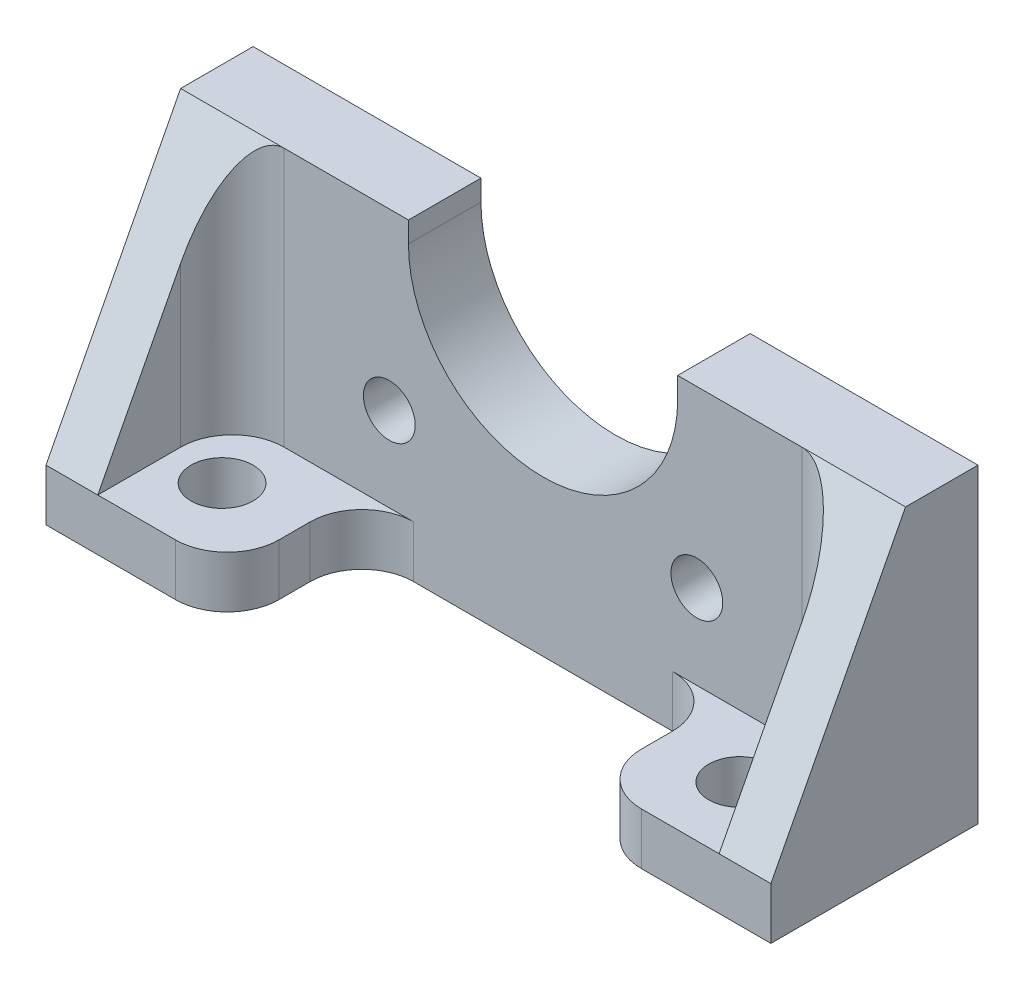
SolidWorks part; units mm, degrees
ref_plane "Front Plane" through (0, 0, 0) normal (0, 0, 1) x (1, 0, 0)
ref_plane "Top Plane" through (0, 0, 0) normal (0, 1, 0) x (1, 0, 0)
ref_plane "Right Plane" through (0, 0, 0) normal (1, 0, 0) x (0, 0, -1)
sketch "Sketch1" plane through (0, 0, 0) normal (0, 0, 1) x (1, 0, 0)
  line L0 (0, 0) -> (0, 5)
  line L1 (0, 5) -> (0, 30)
  line L2 (0, 30) -> (22, 30)
  line L3 (70, 30) -> (70, 5)
  line L4 (70, 5) -> (70, 0)
  line L5 (70, 0) -> (0, 0)
  line L6 (22, 28) -> (22, 30)
  line L7 (48, 28) -> (48, 30)
  line L8 (48, 30) -> (70, 30)
  line L9 (20.1508, 13.1508) -> (35, 28) construction
  line L10 (35, 28) -> (49.8492, 13.1508) construction
  arc A0 (22, 28) -> (48, 28) centre (35, 28) ccw
  circle A1 centre (20.1508, 13.1508) radius 2.5
  circle A2 centre (49.8492, 13.1508) radius 2.5
  circle A3 centre (35, 28) radius 21 construction
  dimension "D1" = 13
  dimension "D7" = 5
  dimension "D8" = 42
  dimension "D2" = 5
  dimension "D3" = 70
  dimension "D5" = 2
  dimension "D6" = 25
extrude "Boss-Extrude1" add sketch "Sketch1" along normal blind 20
sketch "Sketch2" plane through (70, 0, 0) normal (1, 0, 0) x (0, 0, -1)
  line L0 (-7, 30) -> (-20, 5)
  line L1 (-20, 30) -> (0, 30) construction
  line L2 (-20, 5) -> (-20, 30)
  line L3 (-20, 30) -> (-7, 30)
  line L4 (0, 0) -> (0, 30) construction
  line L5 (-20, 0) -> (-20, 30) construction
  line L6 (-20, 0) -> (0, 0) construction
  dimension "D1" = 7
  dimension "D2" = 5
extrude "Cut-Extrude1" cut sketch "Sketch2" against normal through all
sketch "Sketch3" plane through (0, 0, 0) normal (0, -1, 0) x (1, 0, 0)
  line L0 (10, 13) -> (60, 13) construction
  line L3 (35, 13) -> (35, 0) construction
  line L4 (0, 0) -> (70, 0) construction
  line L5 (0, 20) -> (70, 20) construction
  line L6 (17.5, 20) -> (52.5, 20)
  line L7 (17.5, 20) -> (17.5, 12)
  line L8 (22.5, 7) -> (47.5, 7)
  line L9 (52.5, 20) -> (52.5, 12)
  line L10 (35, 7) -> (35, 0) construction
  line L11 (0, 0) -> (70, 0) construction
  circle A0 centre (10, 13) radius 3
  circle A1 centre (60, 13) radius 3
  arc A2 (47.5, 7) -> (52.5, 12) centre (47.5, 12) ccw
  arc A3 (17.5, 12) -> (22.5, 7) centre (22.5, 12) ccw
  dimension "D2" = 6
  dimension "D3" = 5
  dimension "D1" = 50
  dimension "D4" = 35
  dimension "D5" = 7
  dimension "D6" = 13
extrude "Cut-Extrude2" cut sketch "Sketch3" against normal through all
sketch "Sketch4" plane through (0, 0, 0) normal (0, -1, 0) x (1, 0, 0)
  line L0 (0, 0) -> (70, 0) construction
  line L1 (0, 20) -> (17.5, 20) construction
  line L2 (0, 20) -> (0, 0) construction
  line L3 (65, 12) -> (65, 20)
  line L4 (70, 20) -> (70, 0) construction
  line L5 (5, 20) -> (5, 12)
  line L6 (65, 20) -> (5, 20)
  line L8 (10, 7) -> (60, 7)
  arc A0 (5, 12) -> (10, 7) centre (10, 12) ccw
  arc A1 (60, 7) -> (65, 12) centre (60, 12) ccw
  dimension "D1" = 10
  dimension "D2" = 7
  dimension "D3" = 5
  dimension "D4" = 5
extrude "Cut-Extrude3" cut sketch "Sketch4" against normal through all from offset 5 offset against normal yes
fillet "Fillet1" radius 5 2 edges at (52.5, 2.5, 20) (17.5, 2.5, 20)
